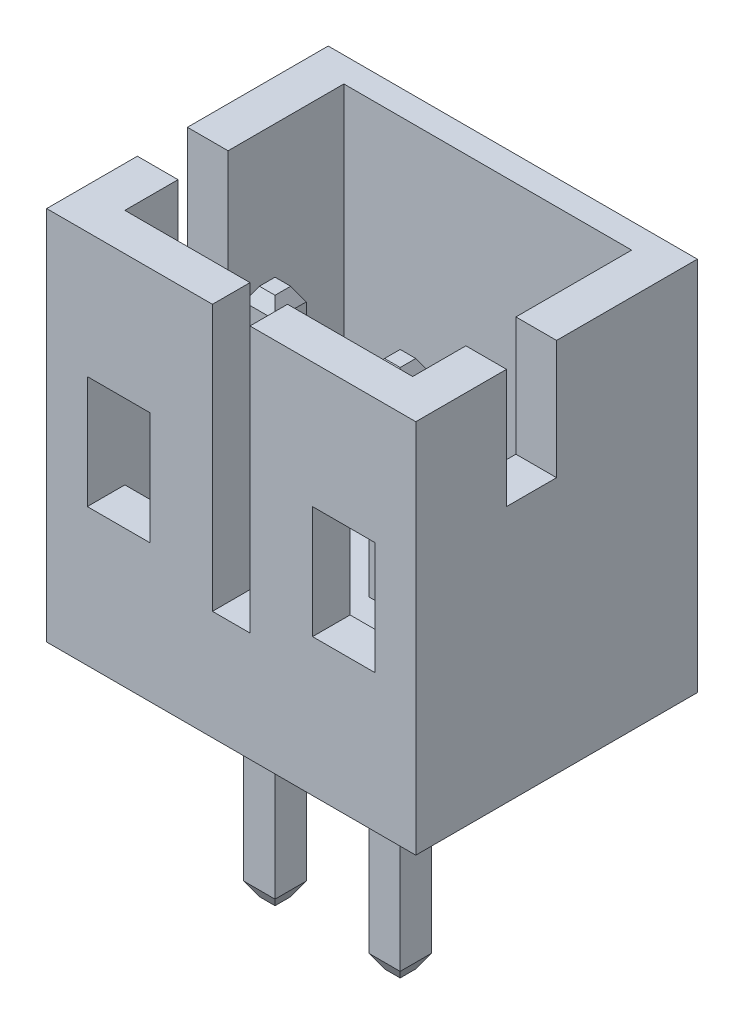
SolidWorks part; units mm, degrees
ref_plane "Front Plane" through (0, 0, 0) normal (0, 0, 1) x (1, 0, 0)
ref_plane "Top Plane" through (0, 0, 0) normal (0, 1, 0) x (1, 0, 0)
ref_plane "Right Plane" through (0, 0, 0) normal (1, 0, 0) x (0, 0, -1)
ref_plane "Plane1" through (4.6, 0, 0) normal (-1, 0, 0) x (0, -1, 0)
sketch "Sketch1" plane through (4.6, 0, 0) normal (-1, 0, 0) x (0, -1, 0)
  line L0 (-6, 4.5) -> (-6, 0.4)
  line L1 (-6, 0.4) -> (0, 0.4)
  line L2 (0, 0.4) -> (0, 4.5)
  line L3 (0, 4.5) -> (-6, 4.5)
extrude "Boss-Extrude1" add sketch "Sketch1" against normal blind 2.6
sketch "Sketch2" plane through (0, 6, 0) normal (0, 1, 0) x (-1, 0, 0)
  line L0 (-4.6, 0.4) -> (-4.6, 3.9)
  line L1 (-4.6, 3.9) -> (-7.2, 3.9)
  line L2 (-7.2, 3.9) -> (-7.2, 0.4)
  line L3 (-7.2, 0.4) -> (-4.6, 0.4)
extrude "Cut-Extrude1" cut sketch "Sketch2" against normal blind 4.25
sketch "Sketch3" plane through (4.6, 0, 0) normal (-1, 0, 0) x (0, 0, 1)
  line L0 (3.9, 1.75) -> (4.5, 1.75)
  line L1 (4.5, 1.75) -> (4.5, 6)
  line L2 (4.5, 6) -> (3.9, 6)
  line L3 (3.9, 6) -> (3.9, 1.75)
extrude "Cut-Extrude2" cut sketch "Sketch3" against normal blind 1.6
sketch "Sketch4" plane through (0, 1.75, 0) normal (0, 1, 0) x (-1, 0, 0)
  line L0 (-4.6, 3.9) -> (-5.6, 3.9)
  line L1 (-5.6, 3.9) -> (-5.6, 4.5)
  line L2 (-5.6, 4.5) -> (-4.6, 4.5)
  line L3 (-4.6, 4.5) -> (-4.6, 3.9)
extrude "Boss-Extrude2" add sketch "Sketch4" along normal blind 4.25
sketch "Sketch5" plane through (4.6, 0, 0) normal (-1, 0, 0) x (0, 0, 1)
  line L0 (0.4, 0) -> (0.4, 1.75)
  line L1 (0.4, 1.75) -> (3.9, 1.75)
  line L2 (3.9, 1.75) -> (3.9, 2.2)
  line L3 (3.9, 2.2) -> (4.5, 2.2)
  line L4 (4.5, 2.2) -> (4.5, 0)
  line L5 (4.5, 0) -> (0.4, 0)
extrude "Boss-Extrude3" add sketch "Sketch5" along normal blind 1
sketch "Sketch6" plane through (4.6, 0, 0) normal (-1, 0, 0) x (0, 0, 1)
  line L0 (4.5, 4) -> (3.9, 4)
  line L1 (3.9, 4) -> (3.9, 6)
  line L2 (3.9, 6) -> (4.5, 6)
  line L3 (4.5, 6) -> (4.5, 4)
extrude "Boss-Extrude4" add sketch "Sketch6" along normal blind 1
sketch "Sketch7" plane through (3.6, 0, 0) normal (-1, 0, 0) x (0, 0, 1)
  line L0 (0.4, 6) -> (4.5, 6)
  line L1 (4.5, 6) -> (4.5, 0)
  line L2 (4.5, 0) -> (0.4, 0)
  line L3 (0.4, 0) -> (0.4, 6)
extrude "Boss-Extrude5" add sketch "Sketch7" along normal blind 0.65
sketch "Sketch8" plane through (7.2, 0, 0) normal (1, 0, 0) x (0, 0, -1)
  line L0 (-3.9, 6) -> (-3.9, 4)
  line L1 (-3.9, 4) -> (-4.5, 4)
  line L2 (-4.5, 4) -> (-4.5, 6)
  line L3 (-4.5, 6) -> (-3.9, 6)
extrude "Boss-Extrude6" add sketch "Sketch8" along normal blind 1
sketch "Sketch9" plane through (7.2, 0, 0) normal (1, 0, 0) x (0, 0, -1)
  line L0 (-3.9, 1.75) -> (-0.4, 1.75)
  line L1 (-0.4, 1.75) -> (-0.4, 0)
  line L2 (-0.4, 0) -> (-4.5, 0)
  line L3 (-4.5, 0) -> (-4.5, 2.2)
  line L4 (-4.5, 2.2) -> (-3.9, 2.2)
  line L5 (-3.9, 2.2) -> (-3.9, 1.75)
extrude "Boss-Extrude7" add sketch "Sketch9" along normal blind 1
sketch "Sketch10" plane through (8.2, 0, 0) normal (1, 0, 0) x (0, 0, -1)
  line L0 (-0.4, 6) -> (-0.4, 0)
  line L1 (-0.4, 0) -> (-4.5, 0)
  line L2 (-4.5, 0) -> (-4.5, 6)
  line L3 (-4.5, 6) -> (-0.4, 6)
extrude "Boss-Extrude8" add sketch "Sketch10" along normal blind 0.65
sketch "Sketch11" plane through (0, 0, 0.4) normal (0, 0, -1) x (-1, 0, 0)
  line L0 (-2.95, 0) -> (-8.85, 0)
  line L1 (-8.85, 0) -> (-8.85, 6)
  line L2 (-8.85, 6) -> (-2.95, 6)
  line L3 (-2.95, 6) -> (-2.95, 0)
extrude "Boss-Extrude9" add sketch "Sketch11" along normal blind 0.4
sketch "Sketch12" plane through (3.6, 0, 0) normal (1, 0, 0) x (0, 0, -1)
  line L0 (-2.25, 6) -> (-3.05, 6)
  line L1 (-3.05, 6) -> (-3.05, 4.1)
  line L2 (-3.05, 4.1) -> (-2.25, 4.1)
  line L3 (-2.25, 4.1) -> (-2.25, 6)
extrude "Cut-Extrude3" cut sketch "Sketch12" against normal through all
sketch "Sketch13" plane through (8.85, 0, 0) normal (1, 0, 0) x (0, 0, -1)
  line L0 (-3.05, 6) -> (-3.05, 4.1)
  line L1 (-3.05, 4.1) -> (-2.25, 4.1)
  line L2 (-2.25, 4.1) -> (-2.25, 6)
  line L3 (-2.25, 6) -> (-3.05, 6)
extrude "Cut-Extrude4" cut sketch "Sketch13" against normal through all
sketch "Sketch14" plane through (0, 1.75, 0) normal (0, 1, 0) x (-1, 0, 0)
  line L0 (-4.65, 2.55) -> (-5.15, 2.55)
  line L1 (-5.15, 2.55) -> (-5.15, 3.05)
  line L2 (-5.15, 3.05) -> (-4.65, 3.05)
  line L3 (-4.65, 3.05) -> (-4.65, 2.55)
extrude "Boss-Extrude10" add sketch "Sketch14" along normal blind 3.3 separate body
sketch "Sketch15" plane through (0, 1.75, 0) normal (0, 1, 0) x (-1, 0, 0)
  line L0 (-6.65, 2.55) -> (-7.15, 2.55)
  line L1 (-7.15, 2.55) -> (-7.15, 3.05)
  line L2 (-7.15, 3.05) -> (-6.65, 3.05)
  line L3 (-6.65, 3.05) -> (-6.65, 2.55)
extrude "Boss-Extrude11" add sketch "Sketch15" along normal blind 3.3 separate body
sketch "Sketch16" plane through (0, 0, 0) normal (0, -1, 0) x (1, 0, 0)
  line L0 (5.15, 3.05) -> (5.15, 2.55)
  line L1 (5.15, 2.55) -> (4.65, 2.55)
  line L2 (4.65, 2.55) -> (4.65, 3.05)
  line L3 (4.65, 3.05) -> (5.15, 3.05)
extrude "Boss-Extrude12" add sketch "Sketch16" along normal blind 3.4 separate body
sketch "Sketch17" plane through (0, 0, 0) normal (0, -1, 0) x (1, 0, 0)
  line L0 (7.15, 3.05) -> (7.15, 2.55)
  line L1 (7.15, 2.55) -> (6.65, 2.55)
  line L2 (6.65, 2.55) -> (6.65, 3.05)
  line L3 (6.65, 3.05) -> (7.15, 3.05)
extrude "Boss-Extrude13" add sketch "Sketch17" along normal blind 3.4 separate body
chamfer "Chamfer1" distance 0.125 angle 60 4 edges at (4.65, 5.05, 2.8) (4.9, 5.05, 2.55) (4.9, 5.05, 3.05) (5.15, 5.05, 2.8)
chamfer "Chamfer2" distance 0.125 angle 60 4 edges at (6.9, 5.05, 2.55) (7.15, 5.05, 2.8) (6.9, 5.05, 3.05) (6.65, 5.05, 2.8)
chamfer "Chamfer3" distance 0.125 angle 60 4 edges at (7.15, -3.4, 2.8) (6.9, -3.4, 2.55) (6.65, -3.4, 2.8) (6.9, -3.4, 3.05)
chamfer "Chamfer4" distance 0.125 angle 60 4 edges at (5.15, -3.4, 2.8) (4.9, -3.4, 2.55) (4.65, -3.4, 2.8) (4.9, -3.4, 3.05)
